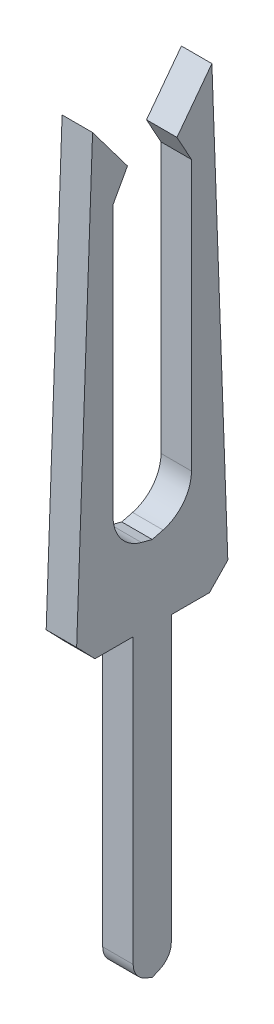
SolidWorks part; units mm, degrees
ref_plane "Front Plane" through (0, 0, 0) normal (0, 0, 1) x (1, 0, 0)
ref_plane "Top Plane" through (0, 0, 0) normal (0, 1, 0) x (1, 0, 0)
ref_plane "Right Plane" through (0, 0, 0) normal (1, 0, 0) x (0, 0, -1)
sketch "Sketch1" plane through (0, 0, 0) normal (1, 0, 0) x (0, 0, -1)
  line L0 (-1.2699, 8.4557) -> (-1.2699, 2.8867) construction
  line L1 (-0.4866, 7.9064) -> (-0.2774, 2.1563)
  line L2 (-0.2774, 2.1563) -> (-0.5184, 1.9064)
  line L3 (-1.2699, -3.2204) -> (-1.2699, 2.8867) construction
  line L4 (-0.5184, 1.9064) -> (-1.0199, 1.9064)
  line L5 (-1.0199, 1.9064) -> (-1.0199, -1.82)
  line L6 (-1.1685, -2.0485) -> (-1.2699, -2.0936)
  line L7 (-1.5949, 7.2969) -> (-2.0533, 7.9064)
  line L8 (-1.2699, 2.8867) -> (-1.128, 2.9239)
  line L9 (-0.7547, 3.4076) -> (-0.7548, 6.9501)
  line L10 (-0.7548, 6.9501) -> (-0.9449, 7.2969)
  line L11 (-0.9449, 7.2969) -> (-0.4866, 7.9064)
  line L12 (-1.7851, 6.9501) -> (-1.5949, 7.2969)
  line L13 (-1.7852, 3.4076) -> (-1.7851, 6.9501)
  line L14 (-1.2699, 2.8867) -> (-1.4119, 2.9239)
  line L15 (-1.3714, -2.0485) -> (-1.2699, -2.0936)
  line L16 (-1.5199, 1.9064) -> (-1.5199, -1.82)
  line L17 (-2.0215, 1.9064) -> (-1.5199, 1.9064)
  line L18 (-2.2625, 2.1563) -> (-2.0215, 1.9064)
  line L19 (-2.0533, 7.9064) -> (-2.2625, 2.1563)
  arc A0 (-1.128, 2.9239) -> (-0.7547, 3.4076) centre (-1.2547, 3.4076) ccw
  arc A1 (-1.0199, -1.82) -> (-1.1685, -2.0485) centre (-1.2699, -1.82) cw
  arc A2 (-1.5199, -1.82) -> (-1.3714, -2.0485) centre (-1.2699, -1.82) ccw
  arc A3 (-1.4119, 2.9239) -> (-1.7852, 3.4076) centre (-1.2852, 3.4076) cw
  point P3 (-0.2684, 1.9064)
  point P28 (-2.2715, 1.9064)
  dimension "D4" = 0.5
  dimension "D5" = 0.25
  dimension "D1" = 6
  dimension "D2" = 4
  dimension "D3" = 0.25
extrude "Boss-Extrude1" add sketch "Sketch1" along normal blind 0.4
